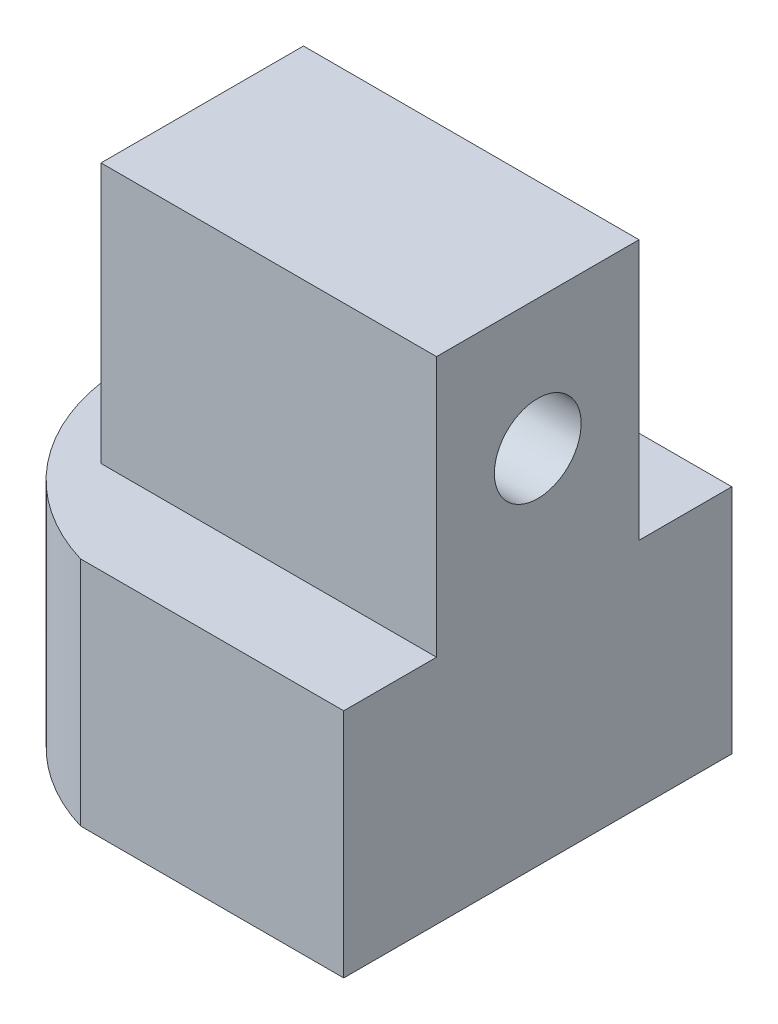
SolidWorks part; units mm, degrees
ref_plane "Спереди" through (0, 0, 0) normal (0, 0, 1) x (1, 0, 0)
ref_plane "Сверху" through (0, 0, 0) normal (0, 1, 0) x (1, 0, 0)
ref_plane "Справа" through (0, 0, 0) normal (1, 0, 0) x (0, 0, -1)
sketch "Sketch1" plane through (0, 0, 0) normal (0, 1, 0) x (1, 0, 0)
  circle A0 centre (0, 0) radius 4
  circle A1 centre (0, 0) radius 7
  dimension "D1" = 8
  dimension "D2" = 14
extrude "Boss-Extrude1" add sketch "Sketch1" along normal blind 6
sketch "Sketch2" plane through (0, 6, 0) normal (0, 1, 0) x (1, 0, 0)
  circle A0 centre (0, 0) radius 7
  circle A1 centre (0, 0) radius 7 construction
extrude "Boss-Extrude2" add sketch "Sketch2" along normal blind 10
sketch "Sketch3" plane through (0, 16, 0) normal (0, 1, 0) x (1, 0, 0)
  line L0 (0, 7) -> (0, -7)
  circle A0 centre (0, 0) radius 7 construction
  arc A1 (0, -7) -> (0, 7) centre (0, 0) cw
extrude "Cut-Extrude1" cut sketch "Sketch3" against normal blind 8
sketch "Sketch4" plane through (0, 0, 0) normal (-1, 0, 0) x (0, 0, 1)
  line L0 (0, 8) -> (0, 16) construction
  line L1 (7, 8) -> (-7, 8) construction
  line L2 (7, 16) -> (-7, 16) construction
  line L4 (2.15, 15.3) -> (-2.15, 15.3)
  line L5 (2.15, 15.3) -> (2.15, 9)
  line L6 (2.15, 9) -> (-2.15, 9)
  line L7 (-2.15, 15.3) -> (-2.15, 9)
  line L8 (2.15, 15.3) -> (-2.15, 9) construction
  line L9 (2.15, 9) -> (-2.15, 15.3) construction
  point P6 (0, 12.15)
  dimension "D1" = 6.3
  dimension "D2" = 4.3
  dimension "D3" = 1
extrude "Cut-Extrude2" cut sketch "Sketch4" against normal blind 6
sketch "Sketch5" plane through (0, 16, 0) normal (0, 1, 0) x (1, 0, 0)
  line L0 (0, 4) -> (5.7446, 4)
  line L1 (0, -7) -> (0, 7) construction
  line L2 (0, -4) -> (5.7446, -4)
  line L3 (0, 4) -> (0, -4)
  arc A0 (0, -7) -> (0, 7) centre (0, 0) ccw construction
  arc A1 (5.7446, 4) -> (5.7446, -4) centre (0, 0) cw
  dimension "D1" = 8
  dimension "D2" = 4
extrude "Cut-Extrude3" cut sketch "Sketch5" against normal up to surface (8 mm away) flip side to cut up to face at (-3.5, 8, 0)
sketch "Sketch7" plane through (0, 8, 0) normal (0, 1, 0) x (1, 0, 0)
  line L0 (0, 7) -> (0, -7) construction
  line L1 (2, 6.7082) -> (2, 11.7082)
  line L2 (2, 11.7082) -> (-2, 11.7082)
  line L3 (-2, 11.7082) -> (-2, 6.7082)
  line L4 (2, -6.7082) -> (2, -11.7082)
  line L5 (2, -11.7082) -> (-2, -11.7082)
  line L6 (-2, -11.7082) -> (-2, -6.7082)
  arc A0 (5.7446, 4) -> (5.7446, -4) centre (0, 0) ccw construction
  arc A1 (2, 6.7082) -> (-2, 6.7082) centre (0, 0) ccw
  arc A2 (2, -6.7082) -> (-2, -6.7082) centre (0, 0) cw
  dimension "D1" = 4
  dimension "D2" = 5
extrude "Boss-Extrude3" add sketch "Sketch7" against normal up to surface (8 mm away) up to face at (0, 0, 7)
sketch "Sketch9" plane through (0, 16, 0) normal (0, 1, 0) x (1, 0, 0)
  line L0 (0, -4) -> (0, 4) construction
  circle A0 centre (0, 0) radius 7
  arc A1 (-2, 6.7082) -> (-2, -6.7082) centre (0, 0) ccw construction
extrude "Cut-Extrude6" cut sketch "Sketch9" against normal up to surface (8 mm away) up to face at (0.5791, 8, 0)
sketch "Sketch10" plane through (0, 8, 0) normal (0, 1, 0) x (1, 0, 0)
  line L1 (-4.5, -3.5) -> (4.5, -3.5)
  line L2 (-4.5, -3.5) -> (-4.5, 3.5)
  line L3 (-4.5, 3.5) -> (4.5, 3.5)
  line L4 (4.5, -3.5) -> (4.5, 3.5)
  line L5 (-4.5, -3.5) -> (4.5, 3.5) construction
  line L6 (-4.5, 3.5) -> (4.5, -3.5) construction
  point P0 (0, 0)
  dimension "D1" = 7
  dimension "D2" = 9
extrude "Boss-Extrude5" add sketch "Sketch10" along normal blind 9
sketch "Sketch11" plane through (-4.5, 0, 0) normal (-1, 0, 0) x (0, 0, 1)
  line L0 (0, 17) -> (0, 8) construction
  line L1 (-3.5, 17) -> (3.5, 17) construction
  line L2 (-3.5, 8) -> (3.5, 8) construction
  line L4 (2.65, 9.85) -> (-2.65, 9.85)
  line L5 (2.65, 9.85) -> (2.65, 15.15)
  line L6 (2.65, 15.15) -> (-2.65, 15.15)
  line L7 (-2.65, 9.85) -> (-2.65, 15.15)
  line L8 (2.65, 9.85) -> (-2.65, 15.15) construction
  line L9 (2.65, 15.15) -> (-2.65, 9.85) construction
  point P6 (0, 12.5)
  dimension "D1" = 5.3
  dimension "D2" = 5.3
extrude "Cut-Extrude7" cut sketch "Sketch11" against normal blind 6
sketch "Sketch13" plane through (0, 8, 0) normal (0, 1, 0) x (1, 0, 0)
  line L0 (2, -6.7082) -> (7.1, -6.7082)
  line L1 (7.1, -6.7082) -> (7.1, 6.7082)
  line L2 (7.1, 6.7082) -> (2, 6.7082)
  arc A0 (2, -6.7082) -> (2, 6.7082) centre (0, 0) ccw construction
  arc A1 (2, 6.7082) -> (2, -6.7082) centre (0, 0) cw
  point P3 (7.1, 0)
  point P10 (7, 0)
  dimension "D1" = 0.1
extrude "Boss-Extrude6" add sketch "Sketch13" against normal up to surface (8 mm away) up to face at (0, 0, 0)
sketch "Sketch14" plane through (4.5, 0, 0) normal (1, 0, 0) x (0, 0, -1)
  line L0 (0, 17) -> (0, 8) construction
  line L1 (-3.5, 17) -> (3.5, 17) construction
  line L2 (-3.5, 8) -> (3.5, 8) construction
  line L4 (-3.5, 8) -> (3.5, 8)
  line L5 (-3.5, 8) -> (-3.5, 17)
  line L6 (-3.5, 17) -> (3.5, 17)
  line L7 (3.5, 8) -> (3.5, 17)
  line L8 (-3.5, 8) -> (3.5, 17) construction
  line L9 (-3.5, 17) -> (3.5, 8) construction
  point P6 (0, 12.5)
extrude "Boss-Extrude7" add sketch "Sketch14" along normal up to surface (2.6 mm away) up to face at (7.1, 4, 0)
sketch "Sketch15" plane through (0, 8, 0) normal (0, 1, 0) x (1, 0, 0)
  line L0 (2, 6.7082) -> (-2, 6.7082)
  line L1 (2, -6.7082) -> (-2, -6.7082)
  line L2 (-2, -6.7082) -> (-2, -11.7082)
  line L3 (-2, -11.7082) -> (2, -11.7082)
  line L4 (2, -11.7082) -> (2, -6.7082)
  line L5 (2, 6.7082) -> (2, 11.7082)
  line L6 (2, 11.7082) -> (-2, 11.7082)
  line L7 (-2, 11.7082) -> (-2, 6.7082)
extrude "Cut-Extrude10" cut sketch "Sketch15" against normal through all
sketch "Sketch16" plane through (1.5, 0, 0) normal (-1, 0, 0) x (0, 0, 1)
  line L0 (0, 15.15) -> (0, 9.85) construction
  line L1 (2.65, 15.15) -> (-2.65, 15.15) construction
  line L2 (-2.65, 9.85) -> (2.65, 9.85) construction
  circle A0 centre (0, 12.5) radius 1.5
  dimension "D1" = 3
extrude "Cut-Extrude11" cut sketch "Sketch16" against normal through all
